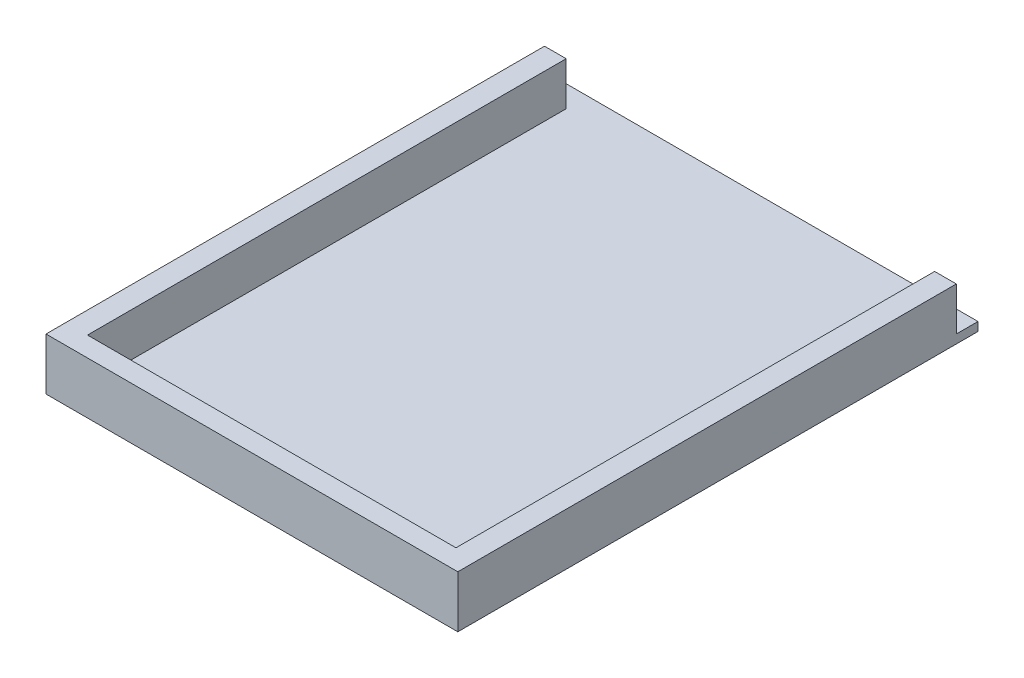
SolidWorks part; units mm, degrees
material "1060 Alloy"
ref_plane "Front Plane" through (0, 0, 0) normal (0, 0, 1) x (1, 0, 0)
ref_plane "Top Plane" through (0, 0, 0) normal (0, 1, 0) x (1, 0, 0)
ref_plane "Right Plane" through (0, 0, 0) normal (1, 0, 0) x (0, 0, -1)
sketch "Sketch1" plane through (0, 0, 0) normal (0, 1, 0) x (1, 0, 0)
  line L1 (-107.95, -139.7) -> (107.95, -139.7)
  line L2 (-107.95, -139.7) -> (-107.95, 139.7)
  line L3 (-107.95, 139.7) -> (107.95, 139.7)
  line L4 (107.95, -139.7) -> (107.95, 139.7)
  line L5 (-107.95, -139.7) -> (107.95, 139.7) construction
  line L6 (-107.95, 139.7) -> (107.95, -139.7) construction
  line L7 (-120.65, -152.4) -> (120.65, -152.4)
  line L8 (-120.65, -152.4) -> (-120.65, 152.4)
  line L9 (-120.65, 152.4) -> (120.65, 152.4)
  line L10 (120.65, -152.4) -> (120.65, 152.4)
  line L11 (-120.65, -152.4) -> (120.65, 152.4) construction
  line L12 (-120.65, 152.4) -> (120.65, -152.4) construction
  point P0 (0, 0)
  point P6 (0, 0)
  dimension "D1" = 279.4
  dimension "D2" = 215.9
  dimension "D3" = 304.8
  dimension "D4" = 241.3
extrude "Boss-Extrude1" add sketch "Sketch1" along normal blind 5.08 contours L1 L4 L3 L2 | L7 L10 L9 L8 L4 L1 L2 L3
sketch "Sketch2" plane through (0, 5.08, 0) normal (0, 1, 0) x (1, 0, 0)
  line L0 (-120.65, 139.7) -> (120.65, 139.7)
  line L1 (-120.65, -152.4) -> (-120.65, 152.4) construction
  line L2 (120.65, -152.4) -> (120.65, 152.4) construction
  line L3 (-120.65, 152.4) -> (120.65, 152.4) construction
  line L4 (-120.65, -152.4) -> (120.65, -152.4) construction
  line L5 (-120.65, -152.4) -> (-120.65, 152.4)
  line L6 (-120.65, 152.4) -> (120.65, 152.4)
  line L7 (120.65, -152.4) -> (120.65, 152.4)
  line L8 (-120.65, -152.4) -> (120.65, -152.4)
  line L9 (-107.95, 139.7) -> (-107.95, -140.7837)
  line L10 (-107.95, -140.7837) -> (107.95, -140.7837)
  line L11 (107.95, -140.7837) -> (107.95, 139.7)
  line M9 (-120.65, -152.4) -> (120.65, -152.4)
  line M10 (120.65, -152.4) -> (120.65, 152.4)
  line M12 (-120.65, 152.4) -> (-120.65, -152.4)
  dimension "D1" = 12.7
  dimension "D2" = 12.7
  dimension "D3" = 12.7
  dimension "D4" = 11.6163
extrude "Boss-Extrude2" add sketch "Sketch2" along normal blind 25.4 contours L11 L10 L9 L0 M12 M9 M10
